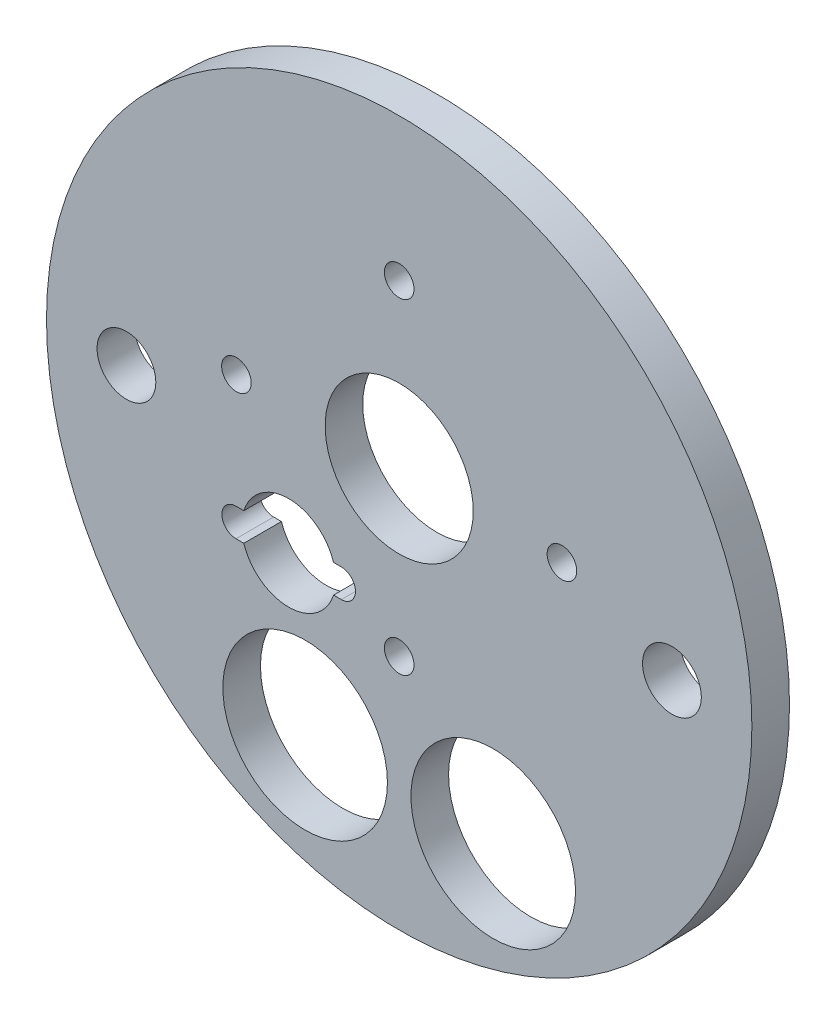
SolidWorks part; units mm, degrees
ref_plane "Front Plane" through (0, 0, 0) normal (0, 0, 1) x (1, 0, 0)
ref_plane "Top Plane" through (0, 0, 0) normal (0, 1, 0) x (1, 0, 0)
ref_plane "Right Plane" through (0, 0, 0) normal (1, 0, 0) x (0, 0, -1)
sketch "Sketch1" plane through (0, 0, 0) normal (0, 0, 1) x (1, 0, 0)
  circle A0 centre (0, 0) radius 49.5046
  dimension "D1" = 99.0092
extrude "Boss-Extrude1" add sketch "Sketch1" along normal blind 5.08
sketch "Sketch2" plane through (0, 0, 5.08) normal (0, 0, 1) x (1, 0, 0)
  circle A0 centre (0, 0) radius 47.625
  dimension "D1" = 95.25
extrude "Boss-Extrude2" add sketch "Sketch2" along normal blind 5.08
sketch "Sketch3" plane through (0, 0, 10.16) normal (0, 0, 1) x (1, 0, 0)
  line L0 (-21.9769, 6.35) -> (0, -15.6269) construction
  line L1 (-21.9769, 6.35) -> (0, 28.3269) construction
  line L2 (0, -15.6269) -> (21.9769, 6.35) construction
  line L3 (0, 28.3269) -> (21.9769, 6.35) construction
  line L4 (-7.8093, -10.9686) -> (-22.0333, -10.9686) construction
  line L5 (-7.8093, -12.8736) -> (-8.8638, -12.8736)
  line L6 (-7.8093, -9.0636) -> (-8.8638, -9.0636)
  line L7 (-20.9789, -12.8736) -> (-22.0333, -12.8736)
  line L8 (-20.9789, -9.0636) -> (-22.0333, -9.0636)
  circle A0 centre (-12.7, -31.1668) radius 11.1125
  circle A1 centre (12.7, -31.1668) radius 11.1125
  circle A2 centre (-12.7, -31.1668) radius 12.7 construction
  circle A3 centre (12.7, -31.1668) radius 12.7 construction
  circle A4 centre (12.7, -31.1668) radius 13.97 construction
  circle A5 centre (-12.7, -31.1668) radius 13.97 construction
  circle A6 centre (0, 0) radius 47.625 construction
  circle A7 centre (-36.83, 0) radius 3.9687
  circle A8 centre (36.83, 0) radius 3.9687
  circle A9 centre (0, 6.35) radius 15.24 construction
  circle A10 centre (-14.9213, -10.9686) radius 8.89 construction
  circle A11 centre (0, 6.35) radius 16.51 construction
  circle A12 centre (-14.9213, -10.9686) radius 7.62 construction
  circle A13 centre (0, 6.35) radius 10
  arc A14 (-20.9789, -12.8736) -> (-8.8638, -12.8736) centre (-14.9213, -10.9686) ccw
  circle A15 centre (0, 28.3269) radius 2
  circle A16 centre (21.9769, 6.35) radius 2
  circle A17 centre (0, -15.6269) radius 2
  circle A18 centre (-21.9769, 6.35) radius 2
  circle A19 centre (0, 6.35) radius 31.55 construction
  arc A24 (-7.8093, -12.8736) -> (-7.8093, -9.0636) centre (-7.8093, -10.9686) ccw
  arc A25 (-22.0333, -9.0636) -> (-22.0333, -12.8736) centre (-22.0333, -10.9686) ccw
  arc A26 (-8.8638, -9.0636) -> (-20.9789, -9.0636) centre (-14.9213, -10.9686) ccw
  point P40 (-14.9213, -10.9686)
  point P47 (-23.9383, -10.9686)
  point P50 (-5.9043, -10.9686)
  point P52 (-14.9213, -10.9686)
  dimension "D1" = 22.225
  dimension "D2" = 22.225
  dimension "D3" = 27.94
  dimension "D4" = 27.94
  dimension "D5" = 25.4
  dimension "D6" = 25.4
  dimension "D7" = 7.9375
  dimension "D8" = 7.9375
  dimension "D11" = 30.48
  dimension "D12" = 33.02
  dimension "D13" = 15.24
  dimension "D14" = 17.78
  dimension "D15" = 20
  dimension "D16" = 12.7
  dimension "D18" = 4
  dimension "D23" = 63.1
  dimension "D9" = 73.66
  dimension "D10" = 36.83
  dimension "D17" = 6.35
  dimension "D19" = 31.08
  dimension "D20" = 31.08
  dimension "D21" = 31.08
  dimension "D27" = 3.81
  dimension "D28" = 18.034
extrude "Cut-Extrude1" cut sketch "Sketch3" against normal through all
sketch "Sketch4" [suppressed] plane through (0, 0, 6.35) normal (0, 0, 1) x (1, 0, 0)
  circle A0 centre (0, 0) radius 49.5046
  circle A1 centre (0, 0) radius 47.6885
extrude "Boss-Extrude3" [suppressed] add sketch "Sketch4" against normal up to surface (3.175 mm away)
sketch "Sketch5" [suppressed] plane through (0, 0, 6.35) normal (0, 0, 1) x (1, 0, 0)
  circle A0 centre (0, 6.35) radius 11.1125
extrude "Boss-Extrude4" [suppressed] add sketch "Sketch5" against normal up to surface (6.35 mm away)
sketch "Sketch6" [suppressed] plane through (0, 0, 6.35) normal (0, 0, 1) x (1, 0, 0)
  circle A0 centre (-23.622, -17.272) radius 2.54
  circle A1 centre (23.622, -17.272) radius 2.54
extrude "Boss-Extrude5" [suppressed] add sketch "Sketch6" against normal blind 6.35
sketch "Sketch7" plane through (0, 0, 0) normal (0, 0, -1) x (-1, 0, 0)
  circle A0 centre (0, 0) radius 52.1663
extrude "Cut-Extrude4" cut sketch "Sketch7" against normal blind 5.08
